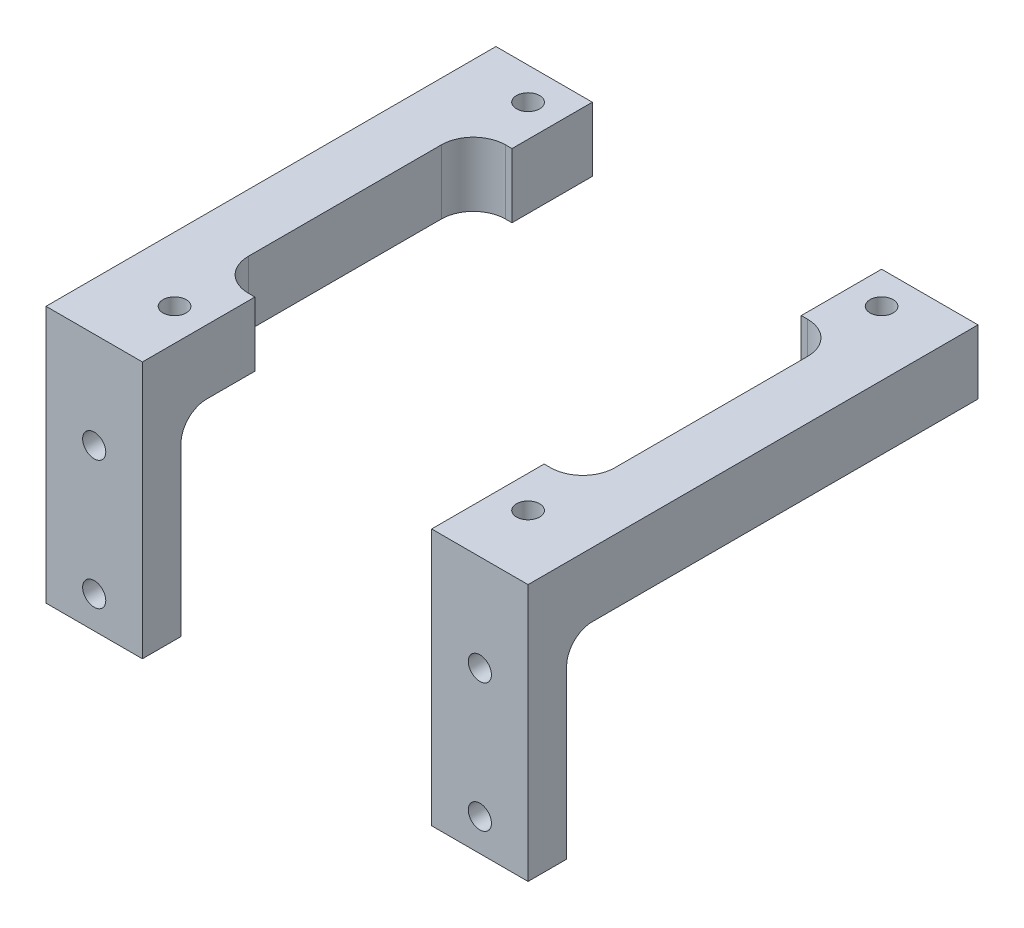
SolidWorks part; units mm, degrees
ref_plane "Front Plane" through (0, 0, 0) normal (0, 0, 1) x (1, 0, 0)
ref_plane "Top Plane" through (0, 0, 0) normal (0, 1, 0) x (1, 0, 0)
ref_plane "Right Plane" through (0, 0, 0) normal (1, 0, 0) x (0, 0, -1)
sketch "Sketch2" plane through (0, 0, 0) normal (0, 0, 1) x (1, 0, 0)
  line L1 (-23.8125, -12.7) -> (23.8125, -12.7)
  line L2 (-23.8125, -12.7) -> (-23.8125, 12.7)
  line L3 (-23.8125, 12.7) -> (23.8125, 12.7)
  line L4 (23.8125, -12.7) -> (23.8125, 12.7)
  line L5 (-23.8125, -12.7) -> (23.8125, 12.7) construction
  line L6 (-23.8125, 12.7) -> (23.8125, -12.7) construction
  point P0 (0, 0)
  dimension "D1" = 25.4
  dimension "D2" = 47.625
extrude "Boss-Extrude1" add sketch "Sketch2" along normal blind 44.45
sketch "Sketch3" plane through (0, 12.7, 0) normal (0, 1, 0) x (1, 0, 0)
  line L0 (0, 0) -> (0, -44.45) construction
  line L1 (23.8125, -44.45) -> (-23.8125, -44.45) construction
  line L2 (23.8125, 0) -> (-23.8125, 0) construction
  line L3 (-14.2875, -44.45) -> (14.2875, -44.45)
  line L4 (-14.2875, -44.45) -> (-14.2875, 0)
  line L5 (-14.2875, 0) -> (14.2875, 0)
  line L6 (14.2875, -44.45) -> (14.2875, 0)
  line L7 (-14.2875, -44.45) -> (14.2875, 0) construction
  line L8 (-14.2875, 0) -> (14.2875, -44.45) construction
  line L9 (23.8125, -44.45) -> (23.8125, 0) construction
  point P5 (0, -22.225)
  dimension "D1" = 9.525
extrude "Cut-Extrude1" cut sketch "Sketch3" against normal through all
sketch "Sketch4" plane through (-23.8125, 0, 0) normal (-1, 0, 0) x (0, 0, 1)
  line L0 (44.45, 12.7) -> (0, 12.7) construction
  line L1 (0, -12.7) -> (40.64, -12.7)
  line L2 (0, -12.7) -> (0, 6.35)
  line L3 (0, 6.35) -> (40.64, 6.35)
  line L4 (40.64, -12.7) -> (40.64, 6.35)
  line L5 (44.45, 12.7) -> (44.45, -12.7) construction
  dimension "D1" = 6.35
  dimension "D2" = 3.81
extrude "Cut-Extrude2" cut sketch "Sketch4" against normal through all
fillet "Fillet1" radius 2.54 1 edges at (19.05, 6.35, 40.64)
fillet "Fillet2" radius 2.54 1 edges at (-19.05, 6.35, 40.64)
sketch "Sketch5" plane through (0, 0, 44.45) normal (0, 0, 1) x (1, 0, 0)
  line L0 (-19.05, 12.7) -> (-19.05, -12.7) construction
  line L3 (-14.2875, 12.7) -> (-23.8125, 12.7) construction
  line L6 (-23.8125, -12.7) -> (-14.2875, -12.7) construction
  line L7 (19.05, -12.7) -> (19.05, 12.7) construction
  line L8 (14.2875, -12.7) -> (23.8125, -12.7) construction
  line L9 (23.8125, 12.7) -> (14.2875, 12.7) construction
  circle A2 centre (-19.05, -9.525) radius 1.143
  circle A3 centre (-19.05, 3.175) radius 1.143
  circle A4 centre (19.05, -9.525) radius 1.143
  circle A5 centre (19.05, 3.175) radius 1.143
  dimension "D1" = 2.286
  dimension "D2" = 2.286
  dimension "D3" = 12.7
  dimension "D4" = 3.175
  dimension "D5" = 12.7
  dimension "D6" = 3.175
  dimension "D7" = 2.286
  dimension "D8" = 2.286
extrude "Cut-Extrude3" cut sketch "Sketch5" against normal through all
sketch "Sketch6" plane through (0, 0, 44.45) normal (0, 0, 1) x (1, 0, 0)
  line L0 (19.05, -12.7) -> (19.05, 12.7) construction
  line L1 (14.2875, -12.7) -> (23.8125, -12.7) construction
  line L2 (23.8125, 12.7) -> (14.2875, 12.7) construction
  circle A1 centre (19.05, -9.525) radius 1.143
  circle A2 centre (19.05, 3.175) radius 1.143
  dimension "D1" = 12.7
  dimension "D2" = 3.175
  dimension "D3" = 2.286
  dimension "D4" = 2.286
extrude "Cut-Extrude4" cut sketch "Sketch6" against normal through all
sketch "Sketch7" plane through (0, 12.7, 0) normal (0, 1, 0) x (1, 0, 0)
  line L0 (0, 0) -> (0, -46.99) construction
  line L1 (-14.2875, 0) -> (-23.8125, 0) construction
  line L2 (-17.4625, -38.1) -> (17.4625, -38.1) construction
  line L3 (-17.4625, -38.1) -> (-17.4625, -3.175) construction
  line L4 (-17.4625, -3.175) -> (17.4625, -3.175) construction
  line L5 (17.4625, -38.1) -> (17.4625, -3.175) construction
  line L6 (-17.4625, -38.1) -> (17.4625, -3.175) construction
  line L7 (-17.4625, -3.175) -> (17.4625, -38.1) construction
  circle A1 centre (-17.4625, -38.1) radius 1.143
  circle A2 centre (17.4625, -38.1) radius 1.143
  circle A3 centre (-17.4625, -3.175) radius 1.143
  circle A4 centre (17.4625, -3.175) radius 1.143
  point P2 (-17.4625, -2.6776)
  point P7 (17.4625, -2.6776)
  point P9 (17.4625, -36.8934)
  point P11 (0, -20.6375)
  point P16 (-17.4625, -37.6132)
  dimension "D4" = 2.286
  dimension "D5" = 2.286
  dimension "D6" = 2.286
  dimension "D7" = 2.286
  dimension "D1" = 34.925
  dimension "D2" = 34.925
  dimension "D3" = 3.175
extrude "Cut-Extrude5" cut sketch "Sketch7" against normal blind 10.16
sketch "Sketch8" plane through (0, 12.7, 0) normal (0, 1, 0) x (1, 0, 0)
  line L0 (0, 0) -> (0, -46.99) construction
  line L1 (-17.4625, -20.6375) -> (17.4625, -20.6375) construction
  line L2 (-17.4625, -3.175) -> (17.4625, -3.175) construction
  line L3 (-17.4625, -3.175) -> (-17.4625, -38.1) construction
  line L4 (-17.4625, -38.1) -> (17.4625, -38.1) construction
  line L5 (17.4625, -3.175) -> (17.4625, -38.1) construction
  line L6 (-14.2875, 0) -> (-14.2875, -44.45) construction
  line L7 (-18.0975, -33.3375) -> (18.0975, -33.3375)
  line L8 (-18.0975, -33.3375) -> (-18.0975, -7.9375)
  line L9 (-18.0975, -7.9375) -> (18.0975, -7.9375)
  line L10 (18.0975, -33.3375) -> (18.0975, -7.9375)
  line L11 (-18.0975, -33.3375) -> (18.0975, -7.9375) construction
  line L12 (-18.0975, -7.9375) -> (18.0975, -33.3375) construction
  point P11 (0, -20.6375)
  dimension "D1" = 3.81
  dimension "D2" = 25.4
extrude "Cut-Extrude6" cut sketch "Sketch8" against normal through all
fillet "Fillet3" radius 3.175 2 edges at (-18.0975, 9.525, 7.9375) (-18.0975, 9.525, 33.3375)
fillet "Fillet4" radius 3.175 2 edges at (18.0975, 9.525, 7.9375) (18.0975, 9.525, 33.3375)
